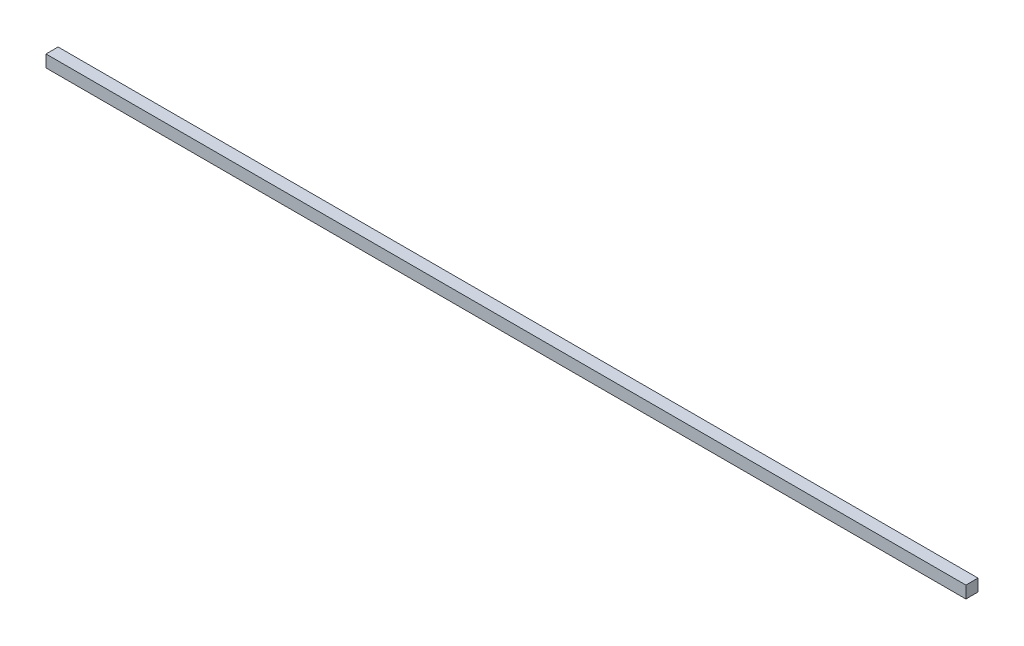
SolidWorks part; units mm, degrees
ref_plane "Front Plane" through (0, 0, 0) normal (0, 0, 1) x (1, 0, 0)
ref_plane "Top Plane" through (0, 0, 0) normal (0, 1, 0) x (1, 0, 0)
ref_plane "Right Plane" through (0, 0, 0) normal (1, 0, 0) x (0, 0, -1)
sketch "Sketch1" plane through (0, 0, 0) normal (0, 1, 0) x (1, 0, 0)
  line L0 (-380, 5) -> (380, -5) construction
  line L1 (-380, 5) -> (380, 5)
  line L2 (-380, 5) -> (-380, -5)
  line L3 (-380, -5) -> (380, -5)
  line L4 (380, 5) -> (380, -5)
  dimension "D1" = 760
  dimension "D2" = 10
extrude "Boss-Extrude1" add sketch "Sketch1" along normal blind 10
